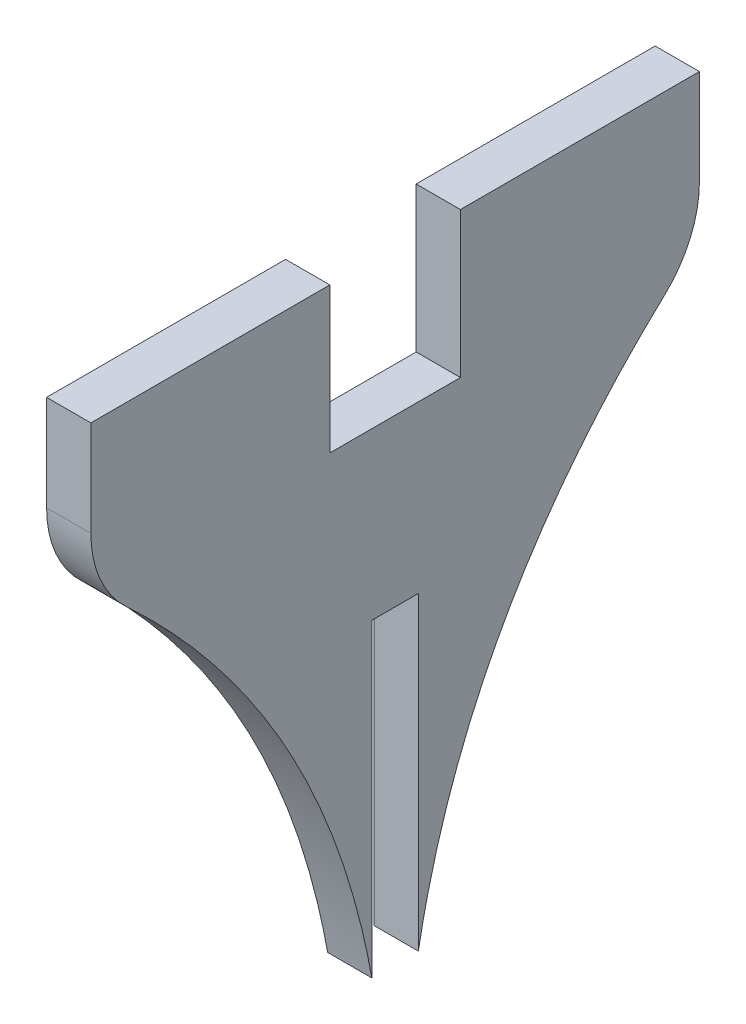
SolidWorks part; units mm, degrees
material "Acier S235"
ref_plane "Plan de face" through (0, 0, 0) normal (0, 0, 1) x (1, 0, 0)
ref_plane "Plan de dessus" through (0, 0, 0) normal (0, 1, 0) x (1, 0, 0)
ref_plane "Plan de droite" through (0, 0, 0) normal (1, 0, 0) x (0, 0, -1)
sketch "Esquisse1" plane through (0, 0, 0) normal (1, 0, 0) x (0, 0, -1)
  line L0 (-27.5, 13.15) -> (-27.5, 0)
  line L1 (-5.9, 13.15) -> (-5.9, 0)
  line L2 (-5.9, 0) -> (5.9, 0)
  line L3 (28.2609, 0) -> (-27.5, 0) construction
  line L4 (-2.1, -15) -> (2.1, -15)
  line L5 (0, -0.2342) -> (0, -65.2342) construction
  line L6 (-27.5, 13.15) -> (-5.9, 13.15)
  line L7 (2.1, -43) -> (2.1, -15)
  line L8 (27.5, 13.15) -> (27.5, 0)
  line L9 (27.5, 13.15) -> (5.9, 13.15)
  line L10 (5.9, 13.15) -> (5.9, 0)
  line L11 (-2.1, -43) -> (-2.1, -15)
  spline S0 degree 2 poles (-27.5, 0) (-6.7362, -17.4604) (-2.1, -43) knots 0 0 0 1 1 1
  spline S1 degree 2 poles (27.5, 0) (6.7362, -17.4604) (2.1, -43) knots 0 0 0 1 1 1
  point P0 (0, 0)
  point P8 (0, -15)
  point P17 (0, 0)
  dimension "D1" = 55
  dimension "D2" = 11.8
  dimension "D3" = 13.15
  dimension "D4" = 4.2
  dimension "D5" = 15
  dimension "D6" = 13
  dimension "D7" = 43
  dimension "D8" = 28
extrude "Boss.-Extru.1" add sketch "Esquisse1" along normal blind 4 contours L6 L1 L2 L10 L9 L8 S1 L7 L4 L11 S0 L0
fillet "Congé1" radius 10 2 edges at (2, 0, -27.5) (2, 0, 27.5)
